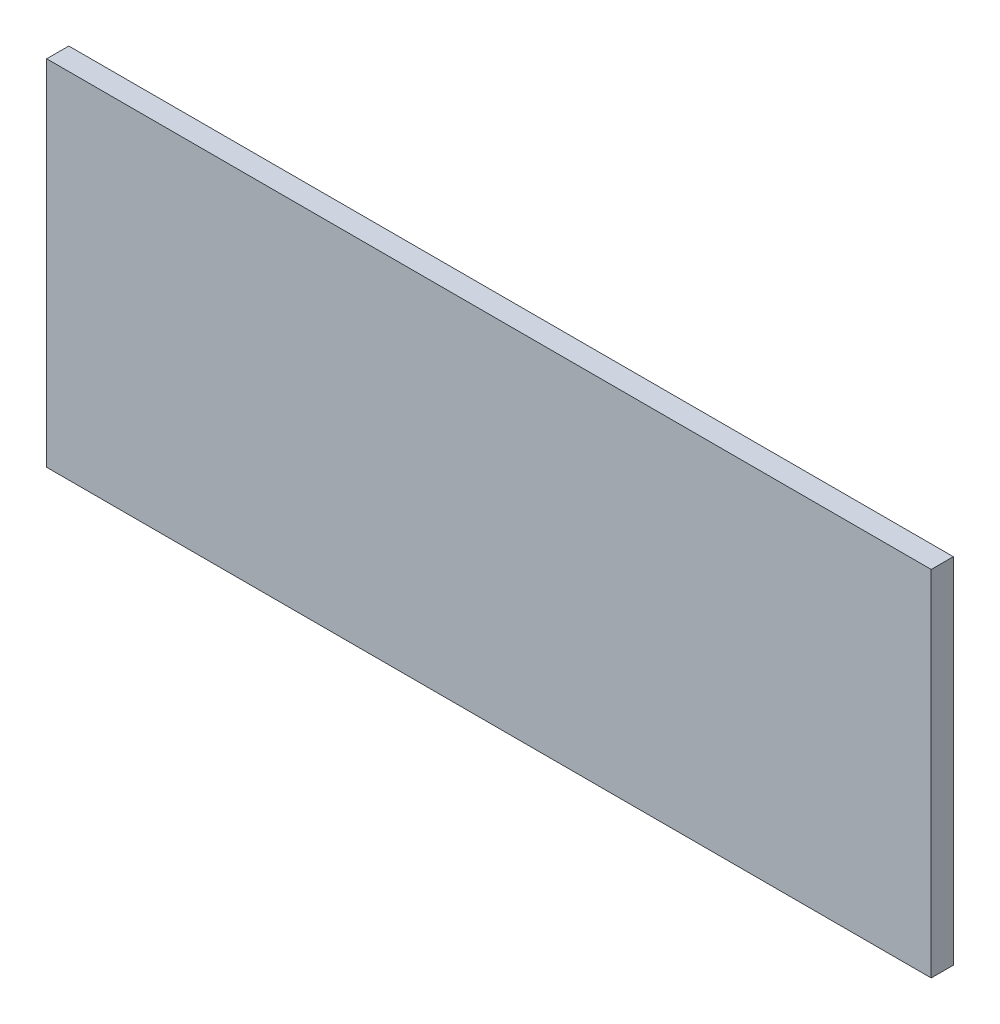
SolidWorks part; units mm, degrees
ref_plane "Front Plane" through (0, 0, 0) normal (0, 0, 1) x (1, 0, 0)
ref_plane "Top Plane" through (0, 0, 0) normal (0, 1, 0) x (1, 0, 0)
ref_plane "Right Plane" through (0, 0, 0) normal (1, 0, 0) x (0, 0, -1)
sketch "Sketch1" plane through (0, 0, 0) normal (0, 0, 1) x (1, 0, 0)
  line L1 (-254, -101.6) -> (254, -101.6)
  line L2 (-254, -101.6) -> (-254, 101.6)
  line L3 (-254, 101.6) -> (254, 101.6)
  line L4 (254, -101.6) -> (254, 101.6)
  line L5 (-254, -101.6) -> (254, 101.6) construction
  line L6 (-254, 101.6) -> (254, -101.6) construction
  point P0 (0, 0)
  dimension "D1" = 203.2
  dimension "D2" = 508
extrude "Boss-Extrude1" add sketch "Sketch1" along normal blind 12.7
